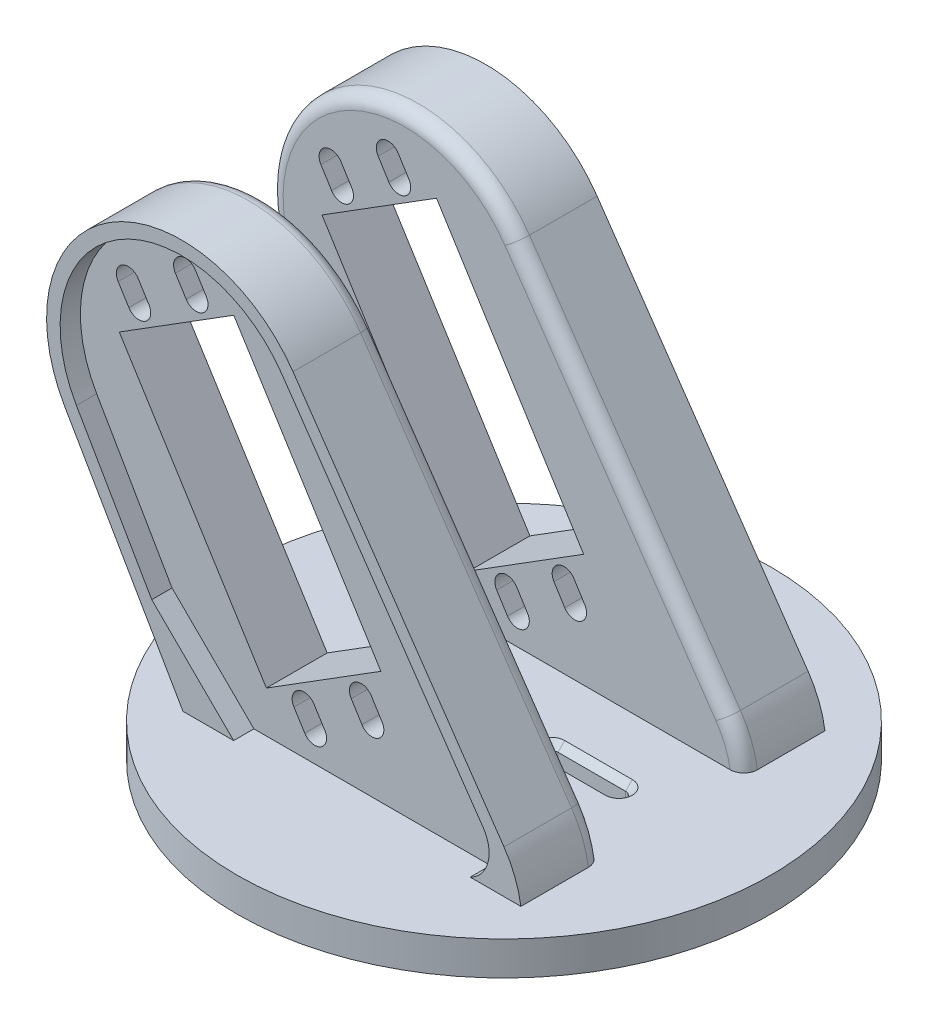
SolidWorks part; units mm, degrees
material "PLA - 20% infill"
ref_plane "Front Plane" through (0, 0, 0) normal (0, 0, 1) x (1, 0, 0)
ref_plane "Top Plane" through (0, 0, 0) normal (0, 1, 0) x (1, 0, 0)
ref_plane "Right Plane" through (0, 0, 0) normal (1, 0, 0) x (0, 0, -1)
sketch "Sketch2" plane through (0, 0, 0) normal (0, 1, 0) x (1, 0, 0)
  circle A0 centre (0, 0) radius 39.5
  dimension "D1" = 79
extrude "Boss-Extrude1" add sketch "Sketch2" along normal blind 5
sketch "Sketch3" plane through (0, 5, 0) normal (0, 1, 0) x (1, 0, 0)
  line L0 (7, 1) -> (17, 1)
  line L1 (7, -1) -> (17, -1)
  line L2 (0, -2.75) -> (0, 2.75) construction
  line L3 (-7, 1) -> (-17, 1)
  line L4 (-7, -1) -> (-17, -1)
  circle A0 centre (0, 0) radius 1.625
  arc A1 (7, 1) -> (7, -1) centre (7, 0) ccw
  arc A2 (17, -1) -> (17, 1) centre (17, 0) ccw
  arc A3 (-17, -1) -> (-17, 1) centre (-17, 0) cw
  arc A4 (-7, 1) -> (-7, -1) centre (-7, 0) cw
  dimension "D1" = 3.25
  dimension "D2" = 1
  dimension "D3" = 7
  dimension "10" = 10
extrude "Cut-Extrude1" cut sketch "Sketch3" against normal up to surface (5 mm away) and the other way through all up to face at (0, 0, 39.5)
sketch "Sketch4" plane through (0, 0, 0) normal (0, -1, 0) x (1, 0, 0)
  line L0 (-32.1201, 0) -> (32.1201, 0) construction
  line L2 (-20, -5) -> (-20, 5)
  line L4 (20, -5) -> (20, 5)
  line L5 (-20, -5) -> (20, 5) construction
  line L6 (-20, 5) -> (20, -5) construction
  line L19 (-20, 5) -> (-5, 5)
  line L20 (0, -20.0103) -> (0, 20.0103) construction
  line L21 (5, 5) -> (20, 5)
  line L22 (5, -5) -> (20, -5)
  line L23 (-20, -5) -> (-5, -5)
  arc A0 (-5, 5) -> (5, 5) centre (0, 1.6834) cw
  arc A1 (-5, -5) -> (5, -5) centre (0, -1.6834) ccw
  point P0 (0, 0)
  point P9 (0, 0)
  point P12 (0, 7.6834)
  point P16 (0, 0)
  dimension "D3" = 6
  dimension "D1" = 40
  dimension "D2" = 10
  dimension "D4" = 10
extrude "Cut-Extrude2" cut sketch "Sketch4" against normal offset from surface (2 mm away) 3 up to face at (-12, 5, 0)
ref_plane "Plane1" through (0, 0, 10.5) normal (0, 0, 1) x (1, 0, 0)
sketch "Sketch5" plane through (0, 0, 10.5) normal (0, 0, 1) x (1, 0, 0)
  line L0 (-25, 5.0002) -> (25, 5.0002)
  line L1 (22.5027, 11.3787) -> (-8.7128, 56.6622)
  line L2 (-42.5, 35.3111) -> (-25, 5.0002)
  arc A0 (25, 5.0002) -> (22.5027, 11.3787) centre (10.1527, 2.8654) ccw
  arc A1 (-8.7128, 56.6622) -> (-42.5, 35.3111) centre (-25.1795, 45.3111) ccw
  point P2 (0, 5.0002)
  dimension "D2" = 20
  dimension "D3" = 15
  dimension "D1" = 5.0002
  dimension "D4" = 55
  dimension "D5" = 35
  dimension "D6" = 50
  dimension "D7" = 120
extrude "Boss-Extrude2" add sketch "Sketch5" along normal blind 12 separate body
sketch "Sketch6" plane through (0, 0, 22.5) normal (0, 0, 1) x (1, 0, 0)
  line L1 (-17.5, 5.0002) -> (17.5, 5.0002)
  line L2 (-25, 5.0002) -> (25, 5.0002) construction
  line L4 (-29.6188, 17.0002) -> (-17.5, 5.0002)
  line L6 (-40.7679, 36.3111) -> (-23.2679, 6.0002)
  line L7 (20.8561, 10.2436) -> (-10.3594, 55.5271)
  line L12 (-40.7679, 36.3111) -> (-29.6188, 17.0002)
  line L13 (19.4186, 12.3289) -> (-10.3594, 55.5271)
  arc A4 (-10.3594, 55.5271) -> (-40.7679, 36.3111) centre (-25.1795, 45.3111) ccw
  arc A5 (-10.3594, 55.5271) -> (-40.7679, 36.3111) centre (-25.1795, 45.3111) ccw
  arc A7 (19.4186, 12.3289) -> (17.5, 5.0002) centre (15.3019, 9.4911) cw
  point P6 (0, 5.0002)
  dimension "D2" = 2
  dimension "D3" = 5
  dimension "D1" = 35
  dimension "D4" = 12
extrude "Cut-Extrude4" cut sketch "Sketch6" against normal blind 3
sketch "Sketch8" plane through (0, 0, 19.5) normal (0, 0, 1) x (1, 0, 0)
  line L0 (-34.7952, 60.5275) -> (0, 5.0002) construction
  line L1 (-37.428, 45.8964) -> (-15.6573, 11.154)
  line L2 (-15.6573, 11.154) -> (1.2902, 21.7739)
  line L3 (1.2902, 21.7739) -> (-20.4805, 56.5163)
  line L4 (-29.1207, 57.5927) -> (-27.5277, 55.0505)
  line L5 (-26.1549, 59.4511) -> (-24.5619, 56.909)
  line L6 (-3.1021, 16.0712) -> (-1.5091, 13.5291)
  line L7 (-0.1363, 17.9297) -> (1.4567, 15.3876)
  line L8 (17.5, 5.0002) -> (-17.5, 5.0002) construction
  line L9 (-20.4805, 56.5163) -> (-37.428, 45.8964)
  line L10 (-36.034, 71.9208) -> (5.9007, 5) construction
  line L11 (-9.5951, 39.1451) -> (-26.5426, 28.5252) construction
  line L12 (39.5, 5) -> (-39.5, 5) construction
  line L13 (-11.5758, 10.7613) -> (-9.9829, 8.2192)
  line L14 (-8.61, 12.6198) -> (-7.017, 10.0776)
  line L15 (-34.6287, 54.1412) -> (-33.0357, 51.5991)
  line L16 (-37.5945, 52.2827) -> (-36.0015, 49.7406)
  arc A0 (-10.3594, 55.5271) -> (-40.7679, 36.3111) centre (-25.1795, 45.3111) ccw construction
  arc A1 (-26.1549, 59.4511) -> (-29.1207, 57.5927) centre (-27.6378, 58.5219) ccw
  arc A2 (-27.5277, 55.0505) -> (-24.5619, 56.909) centre (-26.0448, 55.9798) ccw
  arc A3 (-0.1363, 17.9297) -> (-3.1021, 16.0712) centre (-1.6192, 17.0005) ccw
  arc A4 (-1.5091, 13.5291) -> (1.4567, 15.3876) centre (-0.0262, 14.4583) ccw
  arc A5 (-11.5758, 10.7613) -> (-8.61, 12.6198) centre (-10.0929, 11.6905) cw
  arc A6 (-7.017, 10.0776) -> (-9.9829, 8.2192) centre (-8.5, 9.1484) cw
  arc A7 (-37.5945, 52.2827) -> (-34.6287, 54.1412) centre (-36.1116, 53.212) cw
  arc A8 (-33.0357, 51.5991) -> (-36.0015, 49.7406) centre (-34.5186, 50.6698) cw
  point P23 (-28.9542, 51.2064)
  dimension "D2" = 3
  dimension "D3" = 1.75
  dimension "D6" = 1.75
  dimension "D7" = 23
  dimension "D9" = 23
  dimension "D4" = 5
  dimension "D1" = 20
  dimension "D5" = 3
  dimension "D8" = 41
  dimension "D10" = 11
extrude "Cut-Extrude5" cut sketch "Sketch8" against normal up to surface (9 mm away) up to face at (-7.7197, 25.9457, 10.5)
sketch "Sketch9" plane through (0, 5, 0) normal (0, 1, 0) x (1, 0, 0)
  circle A1 centre (0, 0) radius 3
  dimension "D1" = 6
extrude "Cut-Extrude6" cut sketch "Sketch9" against normal offset from surface (2 mm away) 1 up to face at (12, 2, 0)
fillet "Fillet3" radius 2 4 edges at (24.1203, 8.3339, 10.5) (-33.75, 20.1557, 10.5) (-35.8636, 62.2182, 10.5) (6.895, 34.0205, 10.5)
chamfer "Chamfer6" distance 1 angle 45 8 edges at (12, 5, 1) (18, 5, 0) (6, 5, 0) (12, 5, -1) (-12, 5, 1) (-6, 5, 0) (-18, 5, 0) (-12, 5, -1)
mirror "Mirror1" about plane through (0, 0, 0) normal (0, 0, 1) of bodies 107
